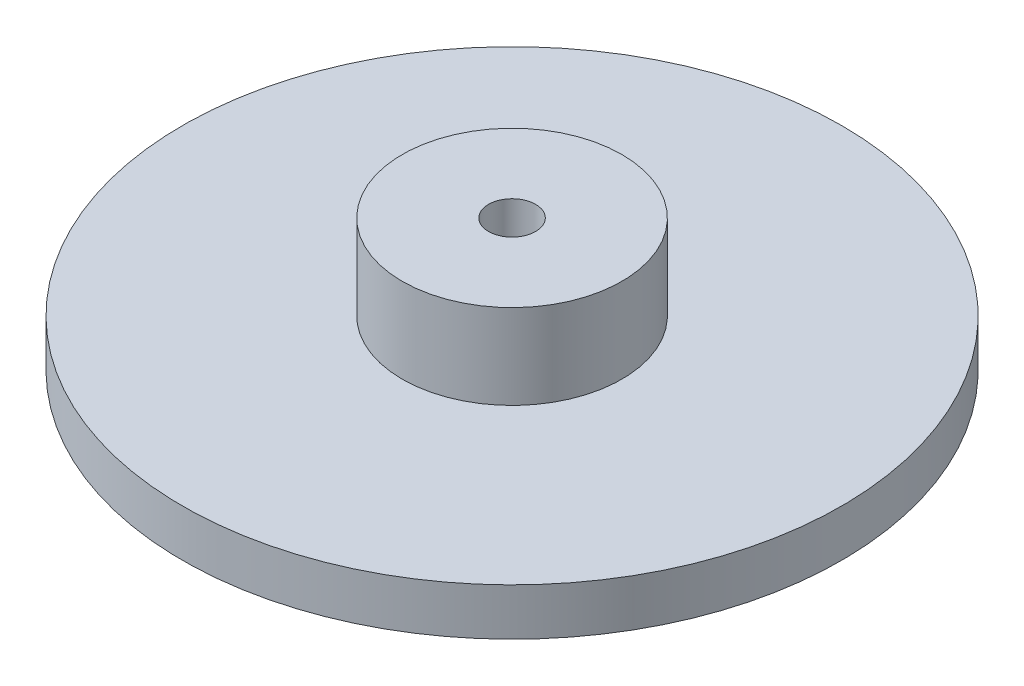
SolidWorks part; units mm, degrees
ref_plane "Plan de face" through (0, 0, 0) normal (0, 0, 1) x (1, 0, 0)
ref_plane "Plan de dessus" through (0, 0, 0) normal (0, 1, 0) x (1, 0, 0)
ref_plane "Plan de droite" through (0, 0, 0) normal (1, 0, 0) x (0, 0, -1)
sketch "Esquisse1" plane through (0, 0, 0) normal (0, 0, 1) x (1, 0, 0)
  line L0 (0, 0) -> (0, 8.4)
  line L1 (0, 8.4) -> (7, 8.4)
  line L2 (7, 8.4) -> (7, 3)
  line L3 (7, 3) -> (21, 3)
  line L4 (21, 3) -> (21, 0)
  line L5 (21, 0) -> (0, 0)
  line L6 (0, 0) -> (0, 13.4441) construction
  dimension "D1" = 7
  dimension "D2" = 21
  dimension "D3" = 3
  dimension "D4" = 5.4
revolve "Révolution1" add sketch "Esquisse1" angle 360 about L6
sketch "Esquisse2" plane through (0, 8.4, 0) normal (0, 1, 0) x (1, 0, 0)
  circle A0 centre (0, 0) radius 1.5
extrude "Enlèv. mat.-Extru.1" cut sketch "Esquisse2" against normal through all
